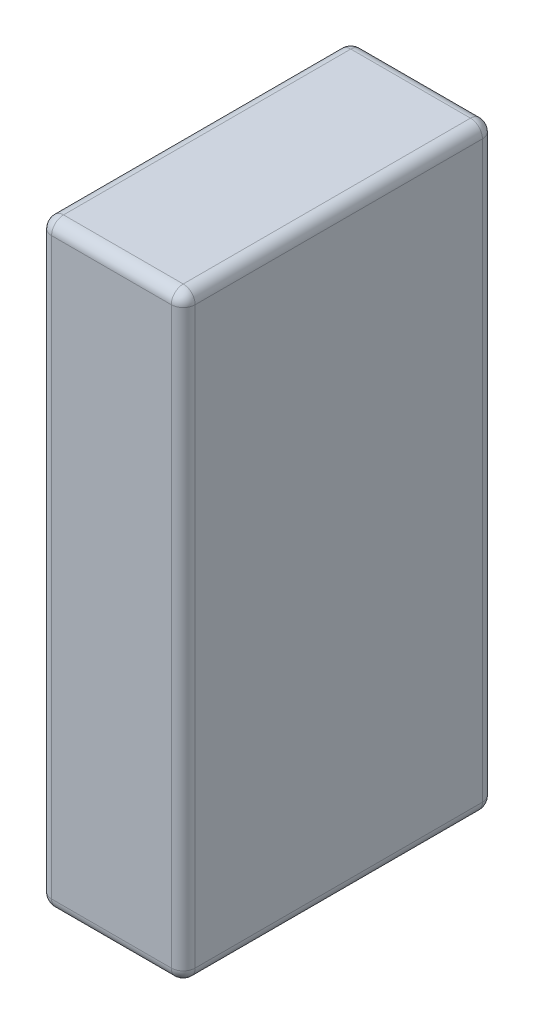
SolidWorks part; units mm, degrees
ref_plane "Plano frontal" through (0, 0, 0) normal (0, 0, 1) x (1, 0, 0)
ref_plane "Plano superior" through (0, 0, 0) normal (0, 1, 0) x (1, 0, 0)
ref_plane "Plano direito" through (0, 0, 0) normal (1, 0, 0) x (0, 0, -1)
sketch "Esboço1" plane through (0, 0, 0) normal (0, 1, 0) x (1, 0, 0)
  line L1 (-60, -130) -> (60, -130)
  line L2 (-60, -130) -> (-60, 130)
  line L3 (-60, 130) -> (60, 130)
  line L4 (60, -130) -> (60, 130)
  line L5 (-60, -130) -> (60, 130) construction
  line L6 (-60, 130) -> (60, -130) construction
  point P0 (0, 0)
  dimension "D1" = 120
  dimension "D2" = 260
extrude "Ressalto-extrusão1" add sketch "Esboço1" along normal blind 500
fillet "Filete1" radius 10 12 edges at (0, 0, -130) (0, 0, 130) (0, 500, 130) (0, 500, -130) (-60, 250, -130) (-60, 500, 0) (-60, 250, 130) (-60, 0, 0) (60, 250, 130) (60, 500, 0) (60, 250, -130) (60, 0, 0)
